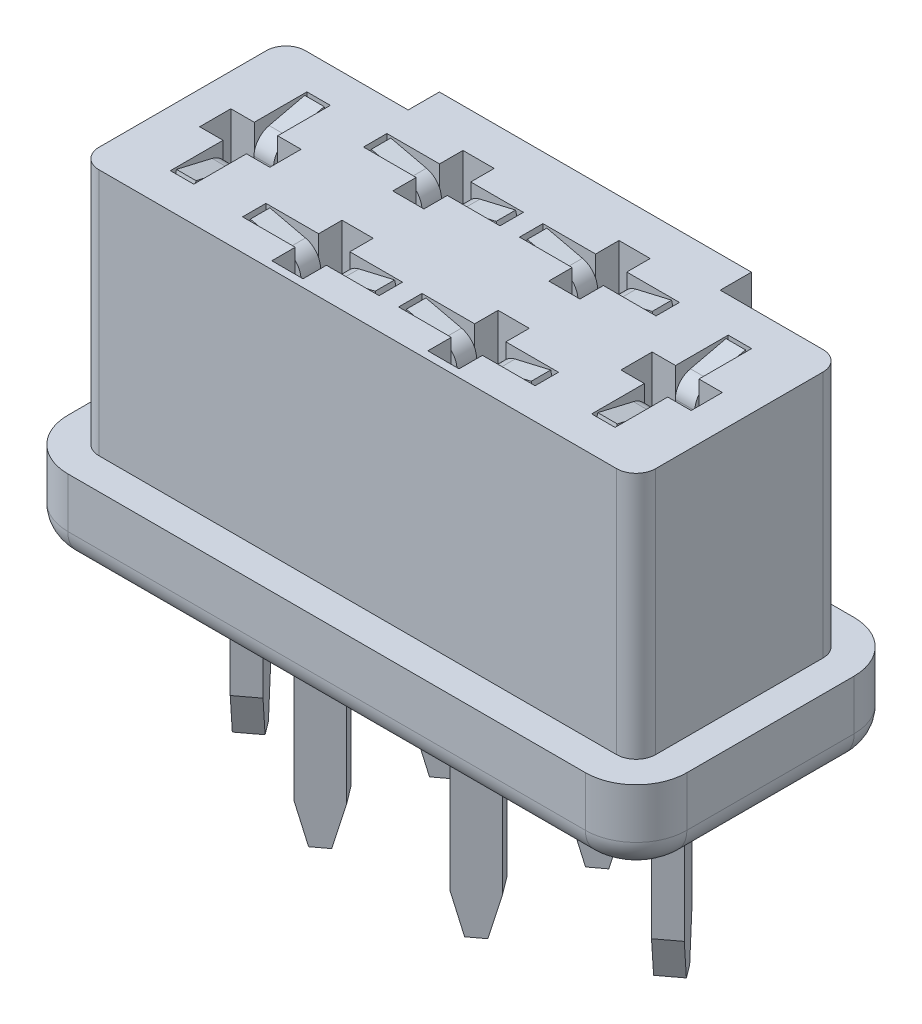
SolidWorks part; units mm, degrees
ref_plane "Front Plane" through (0, 0, 0) normal (0, 0, 1) x (1, 0, 0)
ref_plane "Top Plane" through (0, 0, 0) normal (0, 1, 0) x (1, 0, 0)
ref_plane "Right Plane" through (0, 0, 0) normal (1, 0, 0) x (0, 0, -1)
sketch "Sketch1" plane through (0, 0, 0) normal (0, 1, 0) x (1, 0, 0)
  line L1 (-7.935, 3.445) -> (7.935, 3.445)
  line L2 (-7.935, 3.445) -> (-7.935, -3.445)
  line L3 (-7.935, -3.445) -> (7.935, -3.445)
  line L4 (7.935, 3.445) -> (7.935, -3.445)
  line L5 (-7.935, 3.445) -> (7.935, -3.445) construction
  line L6 (-7.935, -3.445) -> (7.935, 3.445) construction
  point P0 (0, 0)
  dimension "D1" = 6.89
  dimension "D2" = 15.87
extrude "Boss-Extrude1" add sketch "Sketch1" along normal blind 8.38
fillet "Fillet1" radius 1.3 4 edges at (-7.935, 4.19, 3.445) (-7.935, 4.19, -3.445) (7.935, 4.19, -3.445) (7.935, 4.19, 3.445)
fillet "Fillet2" radius 0.75 8 edges at (7.5542, 0, 3.0642) (7.935, 0, 0) (7.5542, 0, -3.0642) (0, 0, -3.445) (-7.5542, 0, -3.0642) (-7.935, 0, 0) (-7.5542, 0, 3.0642) (0, 0, 3.445)
sketch "Sketch2" plane through (0, 8.38, 0) normal (0, 1, 0) x (1, 0, 0)
  line L4 (0, 2.645) -> (0, 3.445) construction
  line L5 (6.635, 3.445) -> (-6.635, 3.445) construction
  line L6 (4, 2.645) -> (4, 3.445)
  line L7 (-4, 2.645) -> (-4, 3.445)
  line L8 (-7.135, 2.145) -> (-7.135, -2.145)
  line L9 (-6.635, -2.645) -> (6.635, -2.645)
  line L10 (7.135, -2.145) -> (7.135, 2.145)
  line L11 (6.635, 2.645) -> (-6.635, 2.645)
  line L12 (-7.135, 2.145) -> (-7.135, -2.145)
  line L13 (-6.635, -2.645) -> (6.635, -2.645)
  line L14 (7.135, -2.145) -> (7.135, 2.145)
  line L15 (6.635, 2.645) -> (4, 2.645)
  line L16 (4, 3.445) -> (-4, 3.445)
  line L17 (-4, 2.645) -> (-6.635, 2.645)
  arc A8 (-7.135, -2.145) -> (-6.635, -2.645) centre (-6.635, -2.145) ccw
  arc A9 (6.635, -2.645) -> (7.135, -2.145) centre (6.635, -2.145) ccw
  arc A10 (7.135, 2.145) -> (6.635, 2.645) centre (6.635, 2.145) ccw
  arc A11 (-6.635, 2.645) -> (-7.135, 2.145) centre (-6.635, 2.145) ccw
  arc A12 (-7.135, -2.145) -> (-6.635, -2.645) centre (-6.635, -2.145) ccw
  arc A13 (6.635, -2.645) -> (7.135, -2.145) centre (6.635, -2.145) ccw
  arc A14 (7.135, 2.145) -> (6.635, 2.645) centre (6.635, 2.145) ccw
  arc A15 (-6.635, 2.645) -> (-7.135, 2.145) centre (-6.635, 2.145) ccw
  dimension "D1" = 0.8
  dimension "D2" = 4
  dimension "D3" = 4
extrude "Cut-Extrude1" cut sketch "Sketch2" against normal blind 6.35 flip side to cut
sketch "Sketch3" plane through (0, 8.38, 0) normal (0, 1, 0) x (1, 0, 0)
  line L0 (0, 3.445) -> (0, -3.445) construction
  line L1 (4, 3.445) -> (-4, 3.445) construction
  line L2 (-6.635, -3.445) -> (6.635, -3.445) construction
  line L3 (-7.135, 0) -> (7.135, 0) construction
  line L4 (-7.135, 2.145) -> (-7.135, -2.145) construction
  line L5 (7.135, -2.145) -> (7.135, 2.145) construction
  line L6 (-2.4, -0.65) -> (-2.4, -1.25)
  line L7 (-2.4, -1.25) -> (-3.75, -1.25)
  line L8 (-3.75, -1.25) -> (-3.75, -1.85)
  line L9 (-3.75, -1.85) -> (-2.4, -1.85)
  line L10 (-2.4, -1.85) -> (-2.4, -2.45)
  line L11 (-2.4, -2.45) -> (-1.6, -2.45)
  line L12 (-1.6, -2.45) -> (-1.6, -1.85)
  line L13 (-1.6, -1.85) -> (-0.25, -1.85)
  line L14 (-0.25, -1.85) -> (-0.25, -1.25)
  line L15 (-0.25, -1.25) -> (-1.6, -1.25)
  line L16 (-1.6, -1.25) -> (-1.6, -0.65)
  line L17 (-1.6, -0.65) -> (-2.4, -0.65)
  line L18 (1.6, -0.65) -> (2.4, -0.65)
  line L19 (1.6, -1.25) -> (1.6, -0.65)
  line L20 (0.25, -1.25) -> (1.6, -1.25)
  line L21 (0.25, -1.85) -> (0.25, -1.25)
  line L22 (1.6, -1.85) -> (0.25, -1.85)
  line L23 (1.6, -2.45) -> (1.6, -1.85)
  line L24 (2.4, -2.45) -> (1.6, -2.45)
  line L25 (2.4, -1.85) -> (2.4, -2.45)
  line L26 (3.75, -1.85) -> (2.4, -1.85)
  line L27 (3.75, -1.25) -> (3.75, -1.85)
  line L28 (2.4, -1.25) -> (3.75, -1.25)
  line L29 (2.4, -0.65) -> (2.4, -1.25)
  line L30 (2.4, 0.65) -> (2.4, 1.25)
  line L31 (2.4, 1.25) -> (3.75, 1.25)
  line L32 (3.75, 1.25) -> (3.75, 1.85)
  line L33 (3.75, 1.85) -> (2.4, 1.85)
  line L34 (2.4, 1.85) -> (2.4, 2.45)
  line L35 (2.4, 2.45) -> (1.6, 2.45)
  line L36 (1.6, 2.45) -> (1.6, 1.85)
  line L37 (1.6, 1.85) -> (0.25, 1.85)
  line L38 (0.25, 1.85) -> (0.25, 1.25)
  line L39 (0.25, 1.25) -> (1.6, 1.25)
  line L40 (1.6, 1.25) -> (1.6, 0.65)
  line L41 (1.6, 0.65) -> (2.4, 0.65)
  line L42 (-1.6, 0.65) -> (-2.4, 0.65)
  line L43 (-1.6, 1.25) -> (-1.6, 0.65)
  line L44 (-0.25, 1.25) -> (-1.6, 1.25)
  line L45 (-0.25, 1.85) -> (-0.25, 1.25)
  line L46 (-1.6, 1.85) -> (-0.25, 1.85)
  line L47 (-1.6, 2.45) -> (-1.6, 1.85)
  line L48 (-2.4, 2.45) -> (-1.6, 2.45)
  line L49 (-2.4, 1.85) -> (-2.4, 2.45)
  line L50 (-3.75, 1.85) -> (-2.4, 1.85)
  line L51 (-3.75, 1.25) -> (-3.75, 1.85)
  line L52 (-2.4, 1.25) -> (-3.75, 1.25)
  line L53 (-2.4, 0.65) -> (-2.4, 1.25)
  line L54 (-5.7, 1.75) -> (-5.1, 1.75)
  line L55 (-5.1, 1.75) -> (-5.1, 0.4)
  line L56 (-5.1, 0.4) -> (-4.5, 0.4)
  line L57 (-4.5, 0.4) -> (-4.5, -0.4)
  line L58 (-4.5, -0.4) -> (-5.1, -0.4)
  line L59 (-5.1, -0.4) -> (-5.1, -1.75)
  line L60 (-5.1, -1.75) -> (-5.7, -1.75)
  line L61 (-5.7, -1.75) -> (-5.7, -0.4)
  line L62 (-5.7, -0.4) -> (-6.3, -0.4)
  line L63 (-6.3, -0.4) -> (-6.3, 0.4)
  line L64 (-6.3, 0.4) -> (-5.7, 0.4)
  line L65 (-5.7, 0.4) -> (-5.7, 1.75)
  line L66 (5.7, 0.4) -> (5.7, 1.75)
  line L67 (6.3, 0.4) -> (5.7, 0.4)
  line L68 (6.3, -0.4) -> (6.3, 0.4)
  line L69 (5.7, -0.4) -> (6.3, -0.4)
  line L70 (5.7, -1.75) -> (5.7, -0.4)
  line L71 (5.1, -1.75) -> (5.7, -1.75)
  line L72 (5.1, -0.4) -> (5.1, -1.75)
  line L73 (4.5, -0.4) -> (5.1, -0.4)
  line L74 (4.5, 0.4) -> (4.5, -0.4)
  line L75 (5.1, 0.4) -> (4.5, 0.4)
  line L76 (5.1, 1.75) -> (5.1, 0.4)
  line L77 (5.7, 1.75) -> (5.1, 1.75)
  dimension "D1" = 3.5
  dimension "D2" = 0.8
  dimension "D3" = 0.6
  dimension "D4" = 1.8
  dimension "D5" = 4
  dimension "D6" = 2.5
  dimension "D7" = 10.8
extrude "Cut-Extrude2" cut sketch "Sketch3" against normal blind 3
sketch "Sketch5" plane through (0, 0, 0) normal (0, -1, 0) x (1, 0, 0)
  line L0 (-5.1, 0.4) -> (-5.7, -0.4) construction
  line L1 (-2.4, 1.85) -> (-1.6, 1.25) construction
  line L2 (-2.4, -1.25) -> (-1.6, -1.85) construction
  line L3 (1.6, -1.25) -> (2.4, -1.85) construction
  line L4 (1.6, 1.85) -> (2.4, 1.25) construction
  line L5 (5.7, 0.4) -> (5.1, -0.4) construction
  line L6 (-5.928, -0.204) -> (-5.352, 0.564)
  line L7 (-5.928, -0.204) -> (-5.448, -0.564)
  line L8 (-5.352, 0.564) -> (-4.872, 0.204)
  line L9 (-5.448, -0.564) -> (-4.872, 0.204)
  line L10 (-5.928, -0.204) -> (-4.872, 0.204) construction
  line L11 (-5.352, 0.564) -> (-5.448, -0.564) construction
  line L12 (-2.204, -1.022) -> (-1.436, -1.598)
  line L13 (-2.204, -1.022) -> (-2.564, -1.502)
  line L14 (-1.436, -1.598) -> (-1.796, -2.078)
  line L15 (-2.564, -1.502) -> (-1.796, -2.078)
  line L16 (-2.204, -1.022) -> (-1.796, -2.078) construction
  line L17 (-1.436, -1.598) -> (-2.564, -1.502) construction
  line L18 (-2.204, 2.078) -> (-1.436, 1.502)
  line L19 (-2.204, 2.078) -> (-2.564, 1.598)
  line L20 (-1.436, 1.502) -> (-1.796, 1.022)
  line L21 (-2.564, 1.598) -> (-1.796, 1.022)
  line L22 (-2.204, 2.078) -> (-1.796, 1.022) construction
  line L23 (-1.436, 1.502) -> (-2.564, 1.598) construction
  line L24 (1.796, 2.078) -> (2.564, 1.502)
  line L25 (1.796, 2.078) -> (1.436, 1.598)
  line L26 (2.564, 1.502) -> (2.204, 1.022)
  line L27 (1.436, 1.598) -> (2.204, 1.022)
  line L28 (1.796, 2.078) -> (2.204, 1.022) construction
  line L29 (2.564, 1.502) -> (1.436, 1.598) construction
  line L30 (1.796, -1.022) -> (2.564, -1.598)
  line L31 (1.796, -1.022) -> (1.436, -1.502)
  line L32 (2.564, -1.598) -> (2.204, -2.078)
  line L33 (1.436, -1.502) -> (2.204, -2.078)
  line L34 (1.796, -1.022) -> (2.204, -2.078) construction
  line L35 (2.564, -1.598) -> (1.436, -1.502) construction
  line L36 (4.872, -0.204) -> (5.448, 0.564)
  line L37 (4.872, -0.204) -> (5.352, -0.564)
  line L38 (5.448, 0.564) -> (5.928, 0.204)
  line L39 (5.352, -0.564) -> (5.928, 0.204)
  line L40 (4.872, -0.204) -> (5.928, 0.204) construction
  line L41 (5.448, 0.564) -> (5.352, -0.564) construction
  point P25 (-5.4, 0)
  point P26 (-2, -1.55)
  point P31 (-2, 1.55)
  point P36 (2, 1.55)
  point P41 (2, -1.55)
  point P46 (5.4, 0)
  dimension "D1" = 0.6
  dimension "D2" = 0.96
extrude "Boss-Extrude2" add sketch "Sketch5" along normal blind 4.69
chamfer "Chamfer1" distance 1 angle 15 12 edges at (5.112, -4.69, -0.384) (5.688, -4.69, 0.384) (1.616, -4.69, 1.838) (2.384, -4.69, 1.262) (1.616, -4.69, -1.262) (2.384, -4.69, -1.838) (-2.384, -4.69, -1.262) (-1.616, -4.69, -1.838) (-2.384, -4.69, 1.838) (-1.616, -4.69, 1.262) (-5.112, -4.69, 0.384) (-5.688, -4.69, -0.384)
ref_plane "Plane1" through (0, 0, -1.55) normal (0, 0, -1) x (-1, 0, 0)
sketch "Sketch6" plane through (0, 0, -1.55) normal (0, 0, -1) x (-1, 0, 0)
  line L0 (-0.25, 5.38) -> (-0.25, 8.38) construction
  line L1 (-4, 8.38) -> (4, 8.38) construction
  line L2 (-2.4, 5.38) -> (-1.6, 5.38) construction
  line L3 (-2.3, 5.68) -> (-1.7, 5.68)
  line L4 (-1.7, 5.68) -> (-1.7, 7.68)
  line L5 (-1.3136, 8.1669) -> (-0.4, 8.38)
  line L6 (-0.4, 8.38) -> (-0.3319, 8.0878)
  line L7 (-0.3319, 8.0878) -> (-1.2454, 7.8748)
  line L8 (-1.4, 7.68) -> (-1.4, 5.38)
  line L9 (-1.6, 5.38) -> (-0.25, 5.38) construction
  line L10 (-1.4, 5.38) -> (-2.6, 5.38)
  line L11 (-2.6, 7.68) -> (-2.6, 5.38)
  line L12 (-3.6681, 8.0878) -> (-2.7546, 7.8748)
  line L13 (-3.6, 8.38) -> (-3.6681, 8.0878)
  line L14 (-2.6864, 8.1669) -> (-3.6, 8.38)
  line L15 (-2.4, 6.88) -> (-1.6, 6.88) construction
  line L16 (-2.4, 5.38) -> (-2.4, 8.38) construction
  line L17 (-1.6, 5.38) -> (-1.6, 8.38) construction
  line L18 (-2, 5.38) -> (-2, 8.38) construction
  line L19 (-2.3, 5.68) -> (-2.3, 7.68)
  arc A0 (-1.2454, 7.8748) -> (-1.4, 7.68) centre (-1.2, 7.68) ccw
  arc A1 (-1.7, 7.68) -> (-1.3136, 8.1669) centre (-1.2, 7.68) cw
  arc A2 (-2.3, 7.68) -> (-2.6864, 8.1669) centre (-2.8, 7.68) ccw
  arc A3 (-2.7546, 7.8748) -> (-2.6, 7.68) centre (-2.8, 7.68) cw
  point P34 (-2, 5.68)
  dimension "D3" = 0.2
  dimension "D4" = 0.5
  dimension "D1" = 0.3
  dimension "D2" = 0.3
  dimension "D5" = 0.15
  dimension "D6" = 0.1
  dimension "D7" = 0.7
  dimension "D8" = 0.3
extrude "Boss-Extrude3" add sketch "Sketch6" along normal mid plane 0.5
mirror "Mirror1" about plane through (0, 0, 0) normal (1, 0, 0) of "Boss-Extrude3"
mirror "Mirror2" about plane through (0, 0, 0) normal (0, 0, 1) of "Boss-Extrude3", "Mirror1"
ref_plane "Plane2" through (-5.4, 0, 0) normal (-1, 0, 0) x (0, 0, 1)
ref_plane "Plane3" through (5.4, 0, 0) normal (-1, 0, 0) x (0, 0, 1)
sketch "Sketch7" plane through (-5.4, 0, 0) normal (-1, 0, 0) x (0, 0, 1)
  line L0 (-0.4, 5.38) -> (0.4, 5.38) construction
  line L1 (-2.145, 8.38) -> (2.145, 8.38) construction
  line L3 (-0.3436, 5.68) -> (0.3436, 5.68)
  line L4 (0.3436, 5.68) -> (0.3436, 7.68)
  line L5 (0.73, 8.1669) -> (1.6436, 8.38)
  line L6 (1.6436, 8.38) -> (1.7117, 8.0878)
  line L7 (1.7117, 8.0878) -> (0.7981, 7.8748)
  line L8 (0.6436, 7.68) -> (0.6436, 5.38)
  line L10 (0.6436, 5.38) -> (-0.6436, 5.38)
  line L11 (-0.6436, 7.68) -> (-0.6436, 5.38)
  line L12 (-1.7117, 8.0878) -> (-0.7981, 7.8748)
  line L13 (-1.6436, 8.38) -> (-1.7117, 8.0878)
  line L14 (-0.73, 8.1669) -> (-1.6436, 8.38)
  line L15 (0.1979, 6.9912) -> (-0.1979, 6.9912) construction
  line L18 (0, 5.38) -> (0, 8.4912) construction
  line L19 (-0.3436, 5.68) -> (-0.3436, 7.68)
  arc A0 (0.7981, 7.8748) -> (0.6436, 7.68) centre (0.8436, 7.68) ccw
  arc A1 (0.3436, 7.68) -> (0.73, 8.1669) centre (0.8436, 7.68) cw
  arc A2 (-0.3436, 7.68) -> (-0.73, 8.1669) centre (-0.8436, 7.68) ccw
  arc A3 (-0.7981, 7.8748) -> (-0.6436, 7.68) centre (-0.8436, 7.68) cw
  point P34 (0, 5.68)
  dimension "D3" = 0.2
  dimension "D4" = 0.5
  dimension "D1" = 0.3
  dimension "D2" = 0.3
  dimension "D5" = 1.2871
  dimension "D6" = 0.6871
  dimension "D7" = 3.2871
  dimension "D8" = 0.3
extrude "Boss-Extrude4" add sketch "Sketch7" along normal mid plane 0.5
mirror "Mirror3" about plane through (0, 0, 0) normal (1, 0, 0) of "Boss-Extrude4"
sketch "Sketch8" plane through (0, 0, 0) normal (0, -1, 0) x (1, 0, 0)
  line L0 (-5.0988, 1.59) -> (-5.0988, 1.3849) construction
  line L1 (-5.0988, 1.3849) -> (-5.868, 1.3849) construction
  line L2 (-5.868, 1.3849) -> (-5.868, 1.59) construction
  line L3 (-5.868, 1.59) -> (-5.0988, 1.59) construction
  line L4 (5.4427, 1.5339) -> (5.4427, 1.9763) construction
  line L5 (5.4427, 1.9763) -> (5.5773, 1.9763) construction
  line L6 (5.5773, 1.9763) -> (5.5773, 1.5339) construction
  line L7 (5.5773, 1.5339) -> (6.0196, 1.5339) construction
  line L8 (6.0196, 1.5339) -> (6.0196, 1.3993) construction
  line L9 (6.0196, 1.3993) -> (5.5773, 1.3993) construction
  line L10 (5.5773, 1.3993) -> (5.5773, 0.957) construction
  line L11 (5.5773, 0.957) -> (5.4427, 0.957) construction
  line L12 (5.4427, 0.957) -> (5.4427, 1.3993) construction
  line L13 (5.4427, 1.3993) -> (5.0004, 1.3993) construction
  line L14 (5.0004, 1.3993) -> (5.0004, 1.5339) construction
  line L15 (5.0004, 1.5339) -> (5.4427, 1.5339) construction
  line L16 (-5.0988, 1.59) -> (-5.0988, 1.3849)
  line L17 (-5.0988, 1.3849) -> (-5.868, 1.3849)
  line L18 (-5.868, 1.3849) -> (-5.868, 1.59)
  line L19 (-5.868, 1.59) -> (-5.0988, 1.59)
  line L20 (5.4427, 1.5339) -> (5.4427, 1.9763)
  line L21 (5.4427, 1.9763) -> (5.5773, 1.9763)
  line L22 (5.5773, 1.9763) -> (5.5773, 1.5339)
  line L23 (5.5773, 1.5339) -> (6.0196, 1.5339)
  line L24 (6.0196, 1.5339) -> (6.0196, 1.3993)
  line L25 (6.0196, 1.3993) -> (5.5773, 1.3993)
  line L26 (5.5773, 1.3993) -> (5.5773, 0.957)
  line L27 (5.5773, 0.957) -> (5.4427, 0.957)
  line L28 (5.4427, 0.957) -> (5.4427, 1.3993)
  line L29 (5.4427, 1.3993) -> (5.0004, 1.3993)
  line L30 (5.0004, 1.3993) -> (5.0004, 1.5339)
  line L31 (5.0004, 1.5339) -> (5.4427, 1.5339)
  line L32 (-0.6855, 2.695) -> (-0.6855, -2.695) construction
  line L35 (6.635, 2.695) -> (-6.635, 2.695) construction
  text T0 "MPX" font "Century Gothic" height 1.5
extrude "Boss-Extrude5" add sketch "Sketch8" along normal blind 0.15
